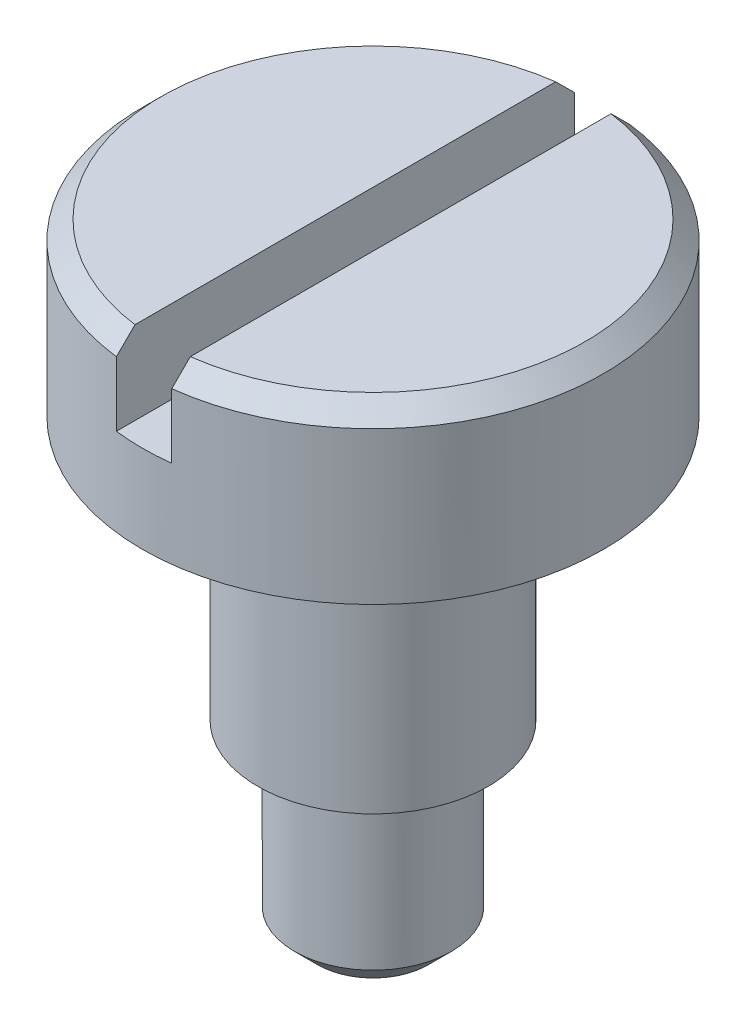
SolidWorks part; units mm, degrees
ref_plane "Front Plane" through (0, 0, 0) normal (0, 0, 1) x (1, 0, 0)
ref_plane "Top Plane" through (0, 0, 0) normal (0, 1, 0) x (1, 0, 0)
ref_plane "Right Plane" through (0, 0, 0) normal (1, 0, 0) x (0, 0, -1)
sketch "Sketch1" plane through (0, 0, 0) normal (0, 1, 0) x (1, 0, 0)
  circle A0 centre (0, 0) radius 2.5
  dimension "D1" = 5
extrude "Boss-Extrude1" add sketch "Sketch1" along normal blind 6.7
sketch "Sketch2" plane through (0, 0, 0) normal (0, -1, 0) x (1, 0, 0)
  circle A0 centre (0, 0) radius 0.85
  dimension "D1" = 1.7
extrude "Cut-Extrude1" cut sketch "Sketch2" against normal blind 2 flip side to cut
cosmetic thread "Cosmetic Thread1" parameters "D2"=1.202
sketch "Sketch3" plane through (0, 2, 0) normal (0, -1, 0) x (1, 0, 0)
  circle A0 centre (0, 0) radius 1.25
  dimension "D1" = 2.5
extrude "Cut-Extrude2" cut sketch "Sketch3" against normal blind 2.85 flip side to cut
chamfer "Chamfer1" distance 0.2 angle 45 1 edges at (0, 6.7, 2.5)
sketch "Sketch4" plane through (0, 0, 0) normal (0, 0, 1) x (1, 0, 0)
  line L0 (0, 0) -> (0, 6.7) construction
  line L1 (2.3, 6.7) -> (-2.3, 6.7) construction
  line L3 (-0.3, 6.7) -> (0.3, 6.7)
  line L4 (-0.3, 6.7) -> (-0.3, 5.8)
  line L5 (-0.3, 5.8) -> (0.3, 5.8)
  line L6 (0.3, 6.7) -> (0.3, 5.8)
  dimension "D1" = 0.6
  dimension "D2" = 0.9
extrude "Cut-Extrude3" cut sketch "Sketch4" against normal through all both and the other way through all
chamfer "Chamfer2" distance 0.25 angle 45 1 edges at (0, 0, -0.85)
fillet "Fillet1" radius 0.1 1 edges at (0, 4.85, -1.25)
